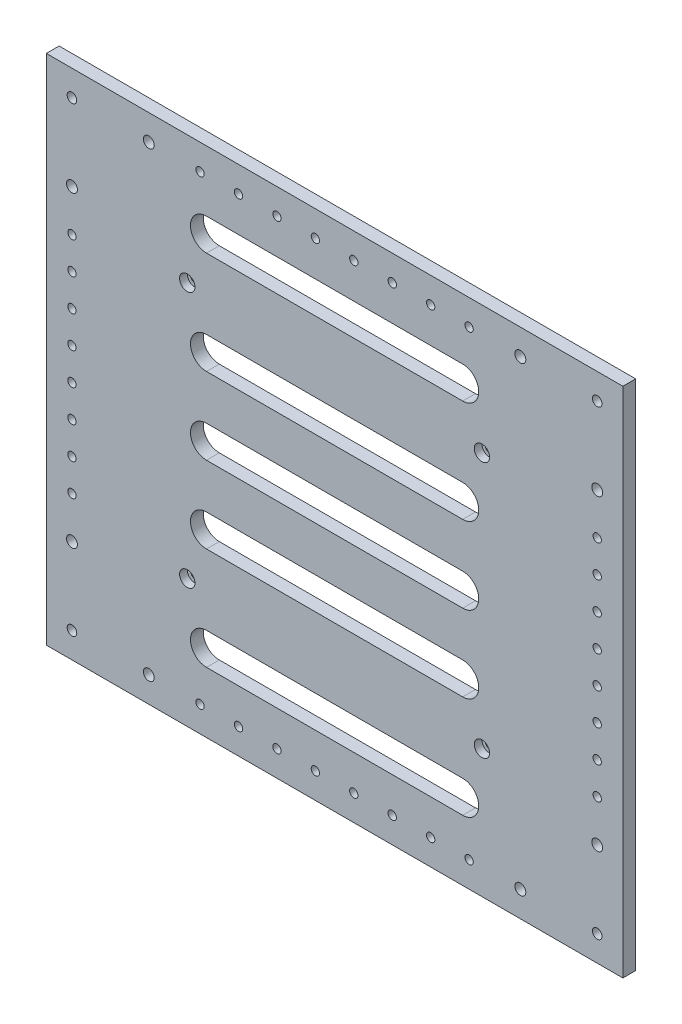
SolidWorks part; units mm, degrees
material "6061-T6 (SS)"
ref_plane "前视基准面" through (0, 0, 0) normal (0, 0, 1) x (1, 0, 0)
ref_plane "上视基准面" through (0, 0, 0) normal (0, 1, 0) x (1, 0, 0)
ref_plane "右视基准面" through (0, 0, 0) normal (1, 0, 0) x (0, 0, -1)
sketch "草图1" plane through (0, 0, 0) normal (0, 0, 1) x (1, 0, 0)
  line L1 (225, -200) -> (-225, -200)
  line L2 (225, -200) -> (225, 200)
  line L3 (225, 200) -> (-225, 200)
  line L4 (-225, -200) -> (-225, 200)
  line L5 (225, -200) -> (-225, 200) construction
  line L6 (225, 200) -> (-225, -200) construction
  line L7 (115, -100) -> (-115, -100) construction
  line L8 (115, -100) -> (115, 100) construction
  line L9 (115, 100) -> (-115, 100) construction
  line L10 (-115, -100) -> (-115, 100) construction
  line L11 (115, -100) -> (-115, 100) construction
  line L12 (115, 100) -> (-115, -100) construction
  circle A0 centre (-115, 100) radius 3.25
  circle A1 centre (115, 100) radius 3.25
  circle A2 centre (115, -100) radius 3.25
  circle A3 centre (-115, -100) radius 3.25
  point P0 (0, 0)
  point P6 (0, 0)
  dimension "D5" = 6.5
  dimension "D6" = 6.5
  dimension "D7" = 6.5
  dimension "D8" = 6.5
  dimension "D1" = 450
  dimension "D2" = 400
  dimension "D3" = 200
  dimension "D4" = 230
extrude "凸台-拉伸1" add sketch "草图1" along normal blind 10
sketch "草图2" plane through (0, 0, 10) normal (0, 0, 1) x (1, 0, 0)
  circle A0 centre (-115, 100) radius 6
  circle A1 centre (115, 100) radius 6
  circle A2 centre (115, -100) radius 6
  circle A3 centre (-115, -100) radius 6
  dimension "D1" = 12
extrude "切除-拉伸1" cut sketch "草图2" against normal blind 6
sketch "草图3" plane through (0, 0, 10) normal (0, 0, 1) x (1, 0, 0)
  line L0 (225, -200) -> (225, 200) construction
  line L1 (-225, -200) -> (225, -200) construction
  line L2 (205, -180) -> (205, -120) construction
  line L3 (145, -180) -> (205, -180) construction
  line L4 (0, 200) -> (0, 0) construction
  line L5 (225, 200) -> (-225, 200) construction
  line L6 (0, 0) -> (-225, 0) construction
  line L7 (-225, 200) -> (-225, -200) construction
  line L8 (145, 180) -> (205, 180) construction
  line L9 (205, 180) -> (205, 120) construction
  line L10 (-205, 180) -> (-205, 120) construction
  line L11 (-145, 180) -> (-205, 180) construction
  line L12 (-145, -180) -> (-205, -180) construction
  line L13 (-205, -180) -> (-205, -120) construction
  circle A0 centre (205, -180) radius 3.75
  circle A1 centre (205, -120) radius 4.25
  circle A2 centre (145, -180) radius 4.25
  circle A3 centre (145, 180) radius 4.25
  circle A4 centre (205, 120) radius 4.25
  circle A5 centre (205, 180) radius 3.75
  circle A6 centre (-205, 180) radius 3.75
  circle A7 centre (-205, 120) radius 4.25
  circle A8 centre (-145, 180) radius 4.25
  circle A9 centre (-145, -180) radius 4.25
  circle A10 centre (-205, -120) radius 4.25
  circle A11 centre (-205, -180) radius 3.75
  dimension "D1" = 7.5
  dimension "D2" = 20
  dimension "D3" = 20
  dimension "D4" = 8.5
  dimension "D5" = 60
  dimension "D6" = 8.5
  dimension "D7" = 60
extrude "切除-拉伸2" cut sketch "草图3" against normal blind 50
sketch "草图4" plane through (0, 0, 10) normal (0, 0, 1) x (1, 0, 0)
  line L0 (225, 0) -> (0, 0) construction
  line L1 (225, -200) -> (225, 200) construction
  line L2 (0, -200) -> (0, 200) construction
  line L3 (225, 200) -> (-225, 200) construction
  line L4 (100, 0) -> (-100, 0) construction
  line L5 (100, -12.5) -> (-100, -12.5)
  line L6 (100, 12.5) -> (-100, 12.5)
  line L7 (100, 60) -> (-100, 60) construction
  line L8 (100, 47.5) -> (-100, 47.5)
  line L9 (100, 72.5) -> (-100, 72.5)
  line L10 (100, -60) -> (-100, -60) construction
  line L11 (100, -47.5) -> (-100, -47.5)
  line L12 (100, -72.5) -> (-100, -72.5)
  line L13 (100, 140) -> (-100, 140) construction
  line L14 (100, 127.5) -> (-100, 127.5)
  line L15 (100, 152.5) -> (-100, 152.5)
  line L16 (100, -140) -> (-100, -140) construction
  line L17 (100, -127.5) -> (-100, -127.5)
  line L18 (100, -152.5) -> (-100, -152.5)
  arc A0 (100, -12.5) -> (100, 12.5) centre (100, 0) ccw
  arc A1 (-100, 12.5) -> (-100, -12.5) centre (-100, 0) ccw
  arc A2 (100, 47.5) -> (100, 72.5) centre (100, 60) ccw
  arc A3 (-100, 72.5) -> (-100, 47.5) centre (-100, 60) ccw
  arc A4 (100, -47.5) -> (100, -72.5) centre (100, -60) cw
  arc A5 (-100, -72.5) -> (-100, -47.5) centre (-100, -60) cw
  arc A6 (100, 127.5) -> (100, 152.5) centre (100, 140) ccw
  arc A7 (-100, 152.5) -> (-100, 127.5) centre (-100, 140) ccw
  arc A8 (100, -127.5) -> (100, -152.5) centre (100, -140) cw
  arc A9 (-100, -152.5) -> (-100, -127.5) centre (-100, -140) cw
  point P10 (0, 0)
  point P19 (0, 60)
  point P25 (0, -60)
  point P32 (0, 140)
  point P39 (0, -140)
  dimension "D2" = 200
  dimension "D1" = 25
  dimension "D4" = 60
  dimension "D6" = 80
  dimension "D3" = 2
  dimension "D5" = 2
extrude "切除-拉伸3" cut sketch "草图4" against normal blind 50
sketch "草图5" plane through (0, 0, 10) normal (0, 0, 1) x (1, 0, 0)
  line L0 (0, -279.7152) -> (0, 279.7152) construction
  line L1 (-145, 180) -> (145, 180) construction
  line L2 (0, 0) -> (272.3125, 0) construction
  line L3 (-145, -180) -> (145, -180) construction
  line L4 (205, 120) -> (205, -124.25) construction
  circle A0 centre (-15, 180) radius 3.25
  circle A1 centre (-45, 180) radius 3.25
  circle A2 centre (-75, 180) radius 3.25
  circle A3 centre (-105, 180) radius 3.25
  circle A4 centre (15, 180) radius 3.25
  circle A5 centre (45, 180) radius 3.25
  circle A6 centre (75, 180) radius 3.25
  circle A7 centre (105, 180) radius 3.25
  circle A8 centre (105, -180) radius 3.25
  circle A9 centre (75, -180) radius 3.25
  circle A10 centre (45, -180) radius 3.25
  circle A11 centre (15, -180) radius 3.25
  circle A12 centre (-105, -180) radius 3.25
  circle A13 centre (-75, -180) radius 3.25
  circle A14 centre (-45, -180) radius 3.25
  circle A15 centre (-15, -180) radius 3.25
  circle A16 centre (205, 12.5) radius 3.25
  circle A17 centre (205, -120) radius 4.25 construction
  circle A18 centre (205, 37.5) radius 3.25
  circle A19 centre (205, 62.5) radius 3.25
  circle A20 centre (205, 87.5) radius 3.25
  circle A21 centre (205, -87.5) radius 3.25
  circle A22 centre (205, -62.5) radius 3.25
  circle A23 centre (205, -37.5) radius 3.25
  circle A24 centre (205, -12.5) radius 3.25
  circle A25 centre (-205, -12.5) radius 3.25
  circle A26 centre (-205, -37.5) radius 3.25
  circle A27 centre (-205, -62.5) radius 3.25
  circle A28 centre (-205, -87.5) radius 3.25
  circle A29 centre (-205, 87.5) radius 3.25
  circle A30 centre (-205, 62.5) radius 3.25
  circle A31 centre (-205, 37.5) radius 3.25
  circle A32 centre (-205, 12.5) radius 3.25
  dimension "D1" = 6.5
  dimension "D2" = 30
  dimension "D4" = 30
  dimension "D5" = 6.5
  dimension "D8" = 25
  dimension "D6" = 25
  dimension "D3" = 4
  dimension "D7" = 4
extrude "切除-拉伸4" cut sketch "草图5" against normal blind 90
